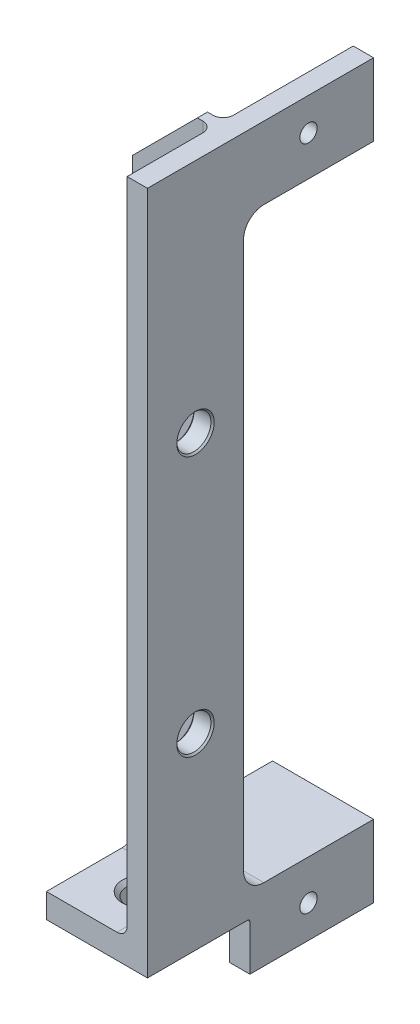
SolidWorks part; units mm, degrees
material "6061-T6 (SS)"
ref_plane "Front Plane" through (0, 0, 0) normal (0, 0, 1) x (1, 0, 0)
ref_plane "Top Plane" through (0, 0, 0) normal (0, 1, 0) x (1, 0, 0)
ref_plane "Right Plane" through (0, 0, 0) normal (1, 0, 0) x (0, 0, -1)
sketch "Sketch1" plane through (0, 0, 0) normal (1, 0, 0) x (0, 0, -1)
  line L0 (0, 0) -> (0, 23.4616) construction
  line L1 (7.5, 0) -> (-7.5, 0) construction
  line L2 (27.813, 57.15) -> (27.813, 45.848)
  line L3 (27.813, 45.848) -> (7.5, 45.848)
  line L4 (7.5, 45.848) -> (7.5, -45.848)
  line L5 (7.5, -45.848) -> (27.813, -45.848)
  line L6 (27.813, -45.848) -> (27.813, -57.15)
  line L7 (27.813, -57.15) -> (8.5, -57.15)
  line L8 (-7.5, -49.658) -> (-7.5, 57.15)
  line L9 (-7.5, 57.15) -> (27.813, 57.15)
  line L10 (8.5, -57.15) -> (8.5, -49.658)
  line L11 (8.5, -49.658) -> (-7.5, -49.658)
  point P15 (0, 0)
  point P16 (7.5, 0)
  dimension "D1" = 3.81
  dimension "D2" = 114.3
  dimension "D3" = 15
  dimension "D4" = 49.658
  dimension "D5" = 27.813
  dimension "D6" = 16
extrude "Boss-Extrude1" add sketch "Sketch1" along normal blind 3.175
sketch "Sketch2" plane through (0, 0, 0) normal (-1, 0, 0) x (0, 0, 1)
  line L0 (7.5, -49.658) -> (7.5, -45.848)
  line L1 (-27.813, -45.848) -> (-7.5, -45.848)
  line L2 (-27.813, -45.848) -> (-27.813, -49.658)
  line L3 (-27.813, -49.658) -> (7.5, -49.658)
  line L4 (7.5, -45.848) -> (-5.9125, -45.848)
  line L5 (7.5, 57.15) -> (7.5, -49.658) construction
  line L6 (-5.9125, 57.15) -> (-7.5, 57.15)
  line L7 (-27.813, 57.15) -> (7.5, 57.15) construction
  line L8 (-5.9125, -45.848) -> (-5.9125, 57.15)
  line L9 (-7.5, -45.848) -> (-7.5, 57.15)
  dimension "D1" = 1.5875
extrude "Boss-Extrude2" add sketch "Sketch2" along normal offset from surface (12.6073 mm away) 15.7823 up to face at (3.175, -9.9316, -12.8252)
sketch "Sketch3" plane through (0, -49.658, 0) normal (0, -1, 0) x (1, 0, 0)
  line L0 (0, 0) -> (-1.8044, 0) construction
  line L1 (3.175, 7.5) -> (3.175, -8.5) construction
  point P0 (-5.1079, 0)
  dimension "D1" = 8.2829
hole_wizard "#10 Clearance Hole1" positions "Sketch5" profile "Sketch4" hole size "#10" standard "Ansi Inch" end condition through all
sketch "Sketch5" plane through (0, -49.658, 0) normal (0, -1, 0) x (1, 0, 0)
  point P0 (-5.1079, 0)
sketch "Sketch4" plane through (-5.1079, -49.658, 0) normal (1, 0, 0) x (0, 0, -1)
  line L0 (0, 0) -> (0, 3.81)
  line L1 (0, 3.81) -> (3.1242, 3.81)
  line L2 (2.4892, 3.175) -> (2.4892, 0.635)
  line L3 (2.4892, 0.635) -> (3.1242, 0)
  line L5 (3.1242, 0) -> (0, 0)
  line L6 (-2.4892, 0.635) -> (-3.1242, 0) construction
  line L7 (3.1242, 3.81) -> (2.4892, 3.175)
  line L8 (-3.1242, 3.81) -> (-2.4892, 3.175) construction
  line L11 (0, -6.35) -> (0, 107.95) construction
  dimension "Thru Hole Dia." = 4.9784
  dimension "Thru Hole Depth" = 3.81
  dimension "Near C'Sink Dia." = 6.2484
  dimension "Near C'Sink Angle" = 90
  dimension "Far C'Sink Dia." = 6.2484
  dimension "Far C'Sink Angle" = 90
fillet "Fillet1" radius 1.5875 1 edges at (-6.3037, -45.848, -5.9125)
fillet "Fillet2" radius 3.175 2 edges at (-4.7162, -45.848, -7.5)
sketch "Sketch6" plane through (0, 0, -7.5) normal (0, 0, -1) x (-1, 0, 0)
  line L0 (2.4473, 57.15) -> (12.6073, 57.15)
  line L1 (12.6073, 57.15) -> (0, 57.15) construction
  line L2 (12.6073, 57.15) -> (12.6073, 46.99)
  line L3 (12.6073, -42.673) -> (12.6073, 57.15) construction
  line L4 (12.6073, 46.99) -> (2.4473, 57.15)
  dimension "D1" = 10.16
extrude "Cut-Extrude1" cut sketch "Sketch6" against normal through all
sketch "Sketch7" plane through (3.175, 0, 0) normal (1, 0, 0) x (0, 0, -1)
  line L3 (0, 0) -> (22.265, 0) construction
  line L4 (27.813, 45.848) -> (27.813, 57.15) construction
  point P3 (17.653, 52.07)
  dimension "D1" = 52.07
  dimension "D2" = 10.16
hole_wizard "#6-32 Tapped Hole1" positions "Sketch9" profile "Sketch8" tap size "#6-32" standard "Ansi Inch" end condition through all
sketch "Sketch9" plane through (3.175, 0, 0) normal (1, 0, 0) x (0, 0, -1)
  point P0 (17.653, 52.07)
sketch "Sketch8" plane through (3.175, 52.07, -17.653) normal (0, 1, 0) x (0, 0, -1)
  line L0 (0, 0) -> (0, 15.7823)
  line L1 (0, 15.7823) -> (1.3525, 15.7823)
  line L2 (1.3525, 15.7823) -> (1.3525, 0)
  line L5 (1.3525, 0) -> (0, 0)
  line L11 (0, -6.35) -> (0, 107.95) construction
  dimension "Thru Tap Drill Dia." = 2.7051
  dimension "Thru Tap Drill Depth" = 15.7823
cosmetic thread "Hole Thread1" parameters "D2"=3.5052
sketch "Sketch10" plane through (0, 0, 0) normal (-1, 0, 0) x (0, 0, 1)
  line L0 (0, 0) -> (22.4066, 0) construction
  line L1 (0, 0) -> (0, 9.2925) construction
  circle A0 centre (0, 20.32) radius 2.667
  dimension "D1" = 5.334
  dimension "D2" = 20.32
extrude "Cut-Extrude2" cut sketch "Sketch10" against normal through all
mirror "Mirror2" about plane through (0, 0, 0) normal (0, 1, 0) of "Cut-Extrude2"
chamfer "Chamfer1" distance 0.254 angle 45 4 edges at (3.175, -20.32, -2.667) (3.175, 20.32, -2.667) (0, 20.32, 2.667) (0, -20.32, 2.667)
fillet "Fillet3" radius 1.5875 5 edges at (0, -45.383, -5.4475)
mirror "Mirror1" about plane through (0, 0, 0) normal (0, 1, 0) of "#6-32 Tapped Hole1"
fillet "Fillet4" radius 0.3962 1 edges
